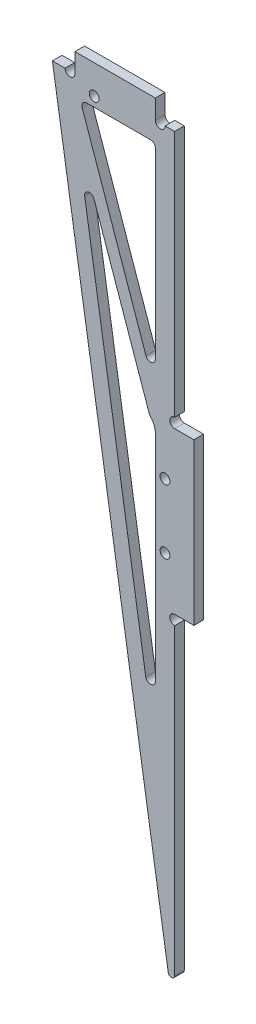
SolidWorks part; units mm, degrees
material "Thornel Mat VMA"
ref_plane "前视基准面" through (0, 0, 0) normal (0, 0, 1) x (1, 0, 0)
ref_plane "上视基准面" through (0, 0, 0) normal (0, 1, 0) x (1, 0, 0)
ref_plane "右视基准面" through (0, 0, 0) normal (1, 0, 0) x (0, 0, -1)
other "Configuration Table"
sketch "草图1" plane through (0, 0, 0) normal (0, 0, 1) x (1, 0, 0)
  line L0 (-38, 0) -> (0, 0)
  line L1 (0, 0) -> (0, -240)
  line L2 (0, -240) -> (-38, 0)
  dimension "D1" = 38
  dimension "D2" = 240
extrude "凸台-拉伸1" add sketch "草图1" along normal blind 3
sketch "草图2" plane through (0, 0, 3) normal (0, 0, 1) x (1, 0, 0)
  circle A0 centre (-25, -3) radius 1.5 construction
  circle A1 centre (-25, -3) radius 1.5 construction
  circle A2 centre (-3, -95) radius 1.5 construction
  circle A3 centre (-3, -115) radius 1.5 construction
  circle A4 centre (-3, -95) radius 1.5 construction
  circle A5 centre (-3, -115) radius 1.5 construction
  circle A6 centre (-3, -115) radius 1.525
  circle A7 centre (-3, -95) radius 1.525
  circle A8 centre (-25, -3) radius 1.525
  dimension "D1" = 3.05
extrude "切除-拉伸1" cut sketch "草图2" against normal blind 40
sketch "草图4" plane through (0, 0, 3) normal (0, 0, 1) x (1, 0, 0)
  line L0 (0, 0) -> (-38, 0) construction
  line L1 (-31, 0) -> (-6, 0)
  line L2 (-31, 0) -> (-31, 6)
  line L3 (-31, 6) -> (-6, 6)
  line L4 (-6, 0) -> (-6, 6)
  line L5 (0, -240) -> (0, 0) construction
  line L6 (0, -80) -> (6, -80)
  line L7 (0, -80) -> (0, -130)
  line L8 (0, -130) -> (6, -130)
  line L9 (6, -80) -> (6, -130)
  circle A0 centre (-3, -115) radius 1.525 construction
  dimension "D1" = 25
  dimension "D2" = 6
  dimension "D3" = 6
  dimension "D4" = 50
  dimension "D5" = 6
  dimension "D6" = 15
extrude "凸台-拉伸2" add sketch "草图4" against normal up to surface (3 mm away) up to face at (-4.525, -115, 0)
sketch "草图5" plane through (0, 0, 0) normal (0, 0, -1) x (-1, 0, 0)
  line L0 (0, -80) -> (0, 0) construction
  line L1 (0, -240) -> (0, -130) construction
  line L2 (0, 0) -> (6, 0) construction
  line L3 (31, 0) -> (38, 0) construction
  circle A0 centre (0, -78.475) radius 1.525
  circle A1 centre (0, -131.525) radius 1.525
  circle A2 centre (4.475, 0) radius 1.525
  circle A3 centre (32.525, 0) radius 1.525
  dimension "D1" = 3.05
extrude "切除-拉伸2" cut sketch "草图5" against normal blind 40
sketch "草图6" plane through (0, 0, 0) normal (0, 0, -1) x (-1, 0, 0)
  line L0 (6, -6) -> (6, -170.1329)
  line L1 (6, -170.1329) -> (31.9877, -6)
  line L2 (31.9877, -6) -> (6, -6)
  line L4 (38, 0) -> (0, -240) construction
  circle A0 centre (3, -95) radius 1.525 construction
  circle A1 centre (25, -3) radius 1.525 construction
  dimension "D1" = 3
  dimension "D2" = 5
  dimension "D3" = 3
extrude "切除-拉伸3" cut sketch "草图6" against normal blind 60
fillet "圆角1" radius 1 1 edges at (0, -240, 1.5)
fillet "圆角2" radius 1.5 3 edges at (-6, -170.1329, 1.5) (-31.9877, -6, 1.5) (-6, -6, 1.5)
sketch "草图7" plane through (0, 0, 0) normal (0, 0, -1) x (-1, 0, 0)
  line L0 (6, -79.2838) -> (31.3721, -6.5258) construction
  line L1 (6, -7.5) -> (6, -151.0675) construction
  line L2 (7.8885, -79.9423) -> (33.2606, -7.1843)
  line L3 (4.1115, -78.6252) -> (29.4836, -5.8673)
  arc A0 (31.7131, -7.7346) -> (30.2315, -6) centre (30.2315, -7.5) ccw construction
  arc A1 (7.8885, -79.9423) -> (4.1115, -78.6252) centre (6, -79.2838) cw
  arc A2 (33.2606, -7.1843) -> (29.4836, -5.8673) centre (31.3721, -6.5258) ccw
  dimension "D1" = 2
  dimension "D2" = 2
extrude "凸台-拉伸3" add sketch "草图7" against normal up to surface (3 mm away) up to face at (-15.0678, -55.055, 3)
fillet "圆角3" radius 5 1 edges at (-6, -81.2838, 1.5)
fillet "圆角4" radius 1.5 3 edges at (-30.5857, -14.855, 1.5) (-6, -73.2098, 1.5) (-29.4374, -6, 1.5)
